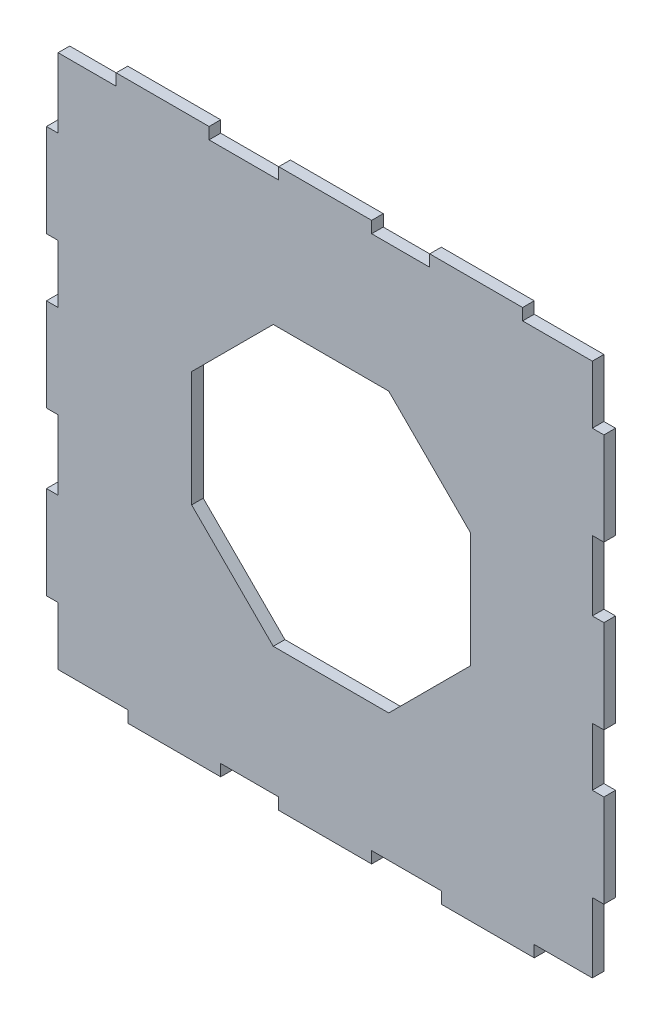
SolidWorks part; units mm, degrees
ref_plane "Front Plane" through (0, 0, 0) normal (0, 0, 1) x (1, 0, 0)
ref_plane "Top Plane" through (0, 0, 0) normal (0, 1, 0) x (1, 0, 0)
ref_plane "Right Plane" through (0, 0, 0) normal (1, 0, 0) x (0, 0, -1)
sketch "Sketch1" plane through (0, 0, 0) normal (0, 0, 1) x (1, 0, 0)
  line L1 (-77.7875, 149.225) -> (74.6125, 149.225)
  line L2 (-77.7875, 149.225) -> (-77.7875, -3.175)
  line L3 (-77.7875, -3.175) -> (74.6125, -3.175)
  line L4 (74.6125, 149.225) -> (74.6125, -3.175)
  line L5 (-55.5625, -3.175) -> (-77.7875, -3.175)
  line L6 (-55.5625, -3.175) -> (-55.5625, 0)
  line L7 (-55.5625, 0) -> (-77.7875, 0)
  line L8 (-77.7875, -3.175) -> (-77.7875, 0)
  line L9 (-77.7875, 15.875) -> (-74.6125, 15.875)
  line L10 (-77.7875, 15.875) -> (-77.7875, -3.175)
  line L11 (-77.7875, -3.175) -> (-74.6125, -3.175)
  line L12 (-74.6125, 15.875) -> (-74.6125, -3.175)
  line L13 (-77.7875, 127) -> (-74.6125, 127)
  line L14 (-77.7875, 127) -> (-77.7875, 149.225)
  line L15 (-77.7875, 149.225) -> (-74.6125, 149.225)
  line L16 (-74.6125, 127) -> (-74.6125, 149.225)
  line L17 (-58.7375, 146.05) -> (-77.7875, 146.05)
  line L18 (-58.7375, 146.05) -> (-58.7375, 149.225)
  line L19 (-58.7375, 149.225) -> (-77.7875, 149.225)
  line L20 (-77.7875, 146.05) -> (-77.7875, 149.225)
  line L21 (52.3875, 149.225) -> (74.6125, 149.225)
  line L22 (52.3875, 149.225) -> (52.3875, 146.05)
  line L23 (52.3875, 146.05) -> (74.6125, 146.05)
  line L24 (74.6125, 149.225) -> (74.6125, 146.05)
  line L25 (74.6125, 130.175) -> (71.4375, 130.175)
  line L26 (74.6125, 130.175) -> (74.6125, 149.225)
  line L27 (74.6125, 149.225) -> (71.4375, 149.225)
  line L28 (71.4375, 130.175) -> (71.4375, 149.225)
  line L29 (71.4375, 19.05) -> (74.6125, 19.05)
  line L30 (71.4375, 19.05) -> (71.4375, -3.175)
  line L31 (71.4375, -3.175) -> (74.6125, -3.175)
  line L32 (74.6125, 19.05) -> (74.6125, -3.175)
  line L33 (55.5625, -3.175) -> (74.6125, -3.175)
  line L34 (55.5625, -3.175) -> (55.5625, 0)
  line L35 (55.5625, 0) -> (74.6125, 0)
  line L36 (74.6125, -3.175) -> (74.6125, 0)
  line L37 (30.1625, -3.175) -> (11.1125, -3.175)
  line L38 (30.1625, -3.175) -> (30.1625, 0)
  line L39 (30.1625, 0) -> (11.1125, 0)
  line L40 (11.1125, -3.175) -> (11.1125, 0)
  line L41 (-14.2875, -3.175) -> (-30.1625, -3.175)
  line L42 (-14.2875, -3.175) -> (-14.2875, 0)
  line L43 (-14.2875, 0) -> (-30.1625, 0)
  line L44 (-30.1625, -3.175) -> (-30.1625, 0)
  line L45 (-77.7875, 41.275) -> (-74.6125, 41.275)
  line L46 (-77.7875, 41.275) -> (-77.7875, 60.325)
  line L47 (-77.7875, 60.325) -> (-74.6125, 60.325)
  line L48 (-74.6125, 41.275) -> (-74.6125, 60.325)
  line L49 (-77.7875, 85.725) -> (-74.6125, 85.725)
  line L50 (-77.7875, 85.725) -> (-77.7875, 101.6)
  line L51 (-77.7875, 101.6) -> (-74.6125, 101.6)
  line L52 (-74.6125, 85.725) -> (-74.6125, 101.6)
  line L53 (-33.3375, 149.225) -> (-14.2875, 149.225)
  line L54 (-33.3375, 149.225) -> (-33.3375, 146.05)
  line L55 (-33.3375, 146.05) -> (-14.2875, 146.05)
  line L56 (-14.2875, 149.225) -> (-14.2875, 146.05)
  line L57 (11.1125, 149.225) -> (26.9875, 149.225)
  line L58 (11.1125, 149.225) -> (11.1125, 146.05)
  line L59 (11.1125, 146.05) -> (26.9875, 146.05)
  line L60 (26.9875, 149.225) -> (26.9875, 146.05)
  line L61 (71.4375, 85.725) -> (74.6125, 85.725)
  line L62 (71.4375, 85.725) -> (71.4375, 104.775)
  line L63 (71.4375, 104.775) -> (74.6125, 104.775)
  line L64 (74.6125, 85.725) -> (74.6125, 104.775)
  line L65 (74.6125, 60.325) -> (71.4375, 60.325)
  line L66 (74.6125, 60.325) -> (74.6125, 44.45)
  line L67 (74.6125, 44.45) -> (71.4375, 44.45)
  line L68 (71.4375, 60.325) -> (71.4375, 44.45)
extrude "Boss-Extrude1" add sketch "Sketch1" along normal blind 3.175 contours L68 L65 L4 L61 L62 L63 L25 L28 L23 L22 L1 L60 L59 L58 L56 L55 L54 L18 L17 L16 L13 L2 L51 L52 L49 L47 L48 L45 L9 L12 L7 L6 L3 L44 L43 L42 L40 L39 L38 L34 L35 L30 L29
sketch "Sketch2" plane through (0, 0, 3.175) normal (0, 0, 1) x (1, 0, 0)
  line L0 (0, 0) -> (0, 132.6708)
  line L1 (-77.7875, 73.025) -> (74.6125, 73.025)
  line L2 (-77.7875, 85.725) -> (-77.7875, 60.325) construction
  line L3 (74.6125, 85.725) -> (74.6125, 60.325) construction
  line L4 (-14.2875, 149.225) -> (11.1125, 149.225) construction
  line L5 (-15.7815, 111.125) -> (-38.1, 88.8065)
  line L6 (-38.1, 88.8065) -> (-38.1, 57.2435)
  line L7 (-38.1, 57.2435) -> (-15.7815, 34.925)
  line L8 (-15.7815, 34.925) -> (15.7815, 34.925)
  line L9 (15.7815, 34.925) -> (38.1, 57.2435)
  line L10 (38.1, 57.2435) -> (38.1, 88.8065)
  line L11 (38.1, 88.8065) -> (15.7815, 111.125)
  line L12 (15.7815, 111.125) -> (-15.7815, 111.125)
  circle A0 centre (0, 73.025) radius 38.1 construction
  dimension "D1" = 38.1
extrude "Cut-Extrude1" cut sketch "Sketch2" against normal through all contours L0 L12 L5 L6 L1 | L11 L12 L0 L1 L10 | L9 L10 L1 L0 L8 | L7 L8 L0 L1 L6
